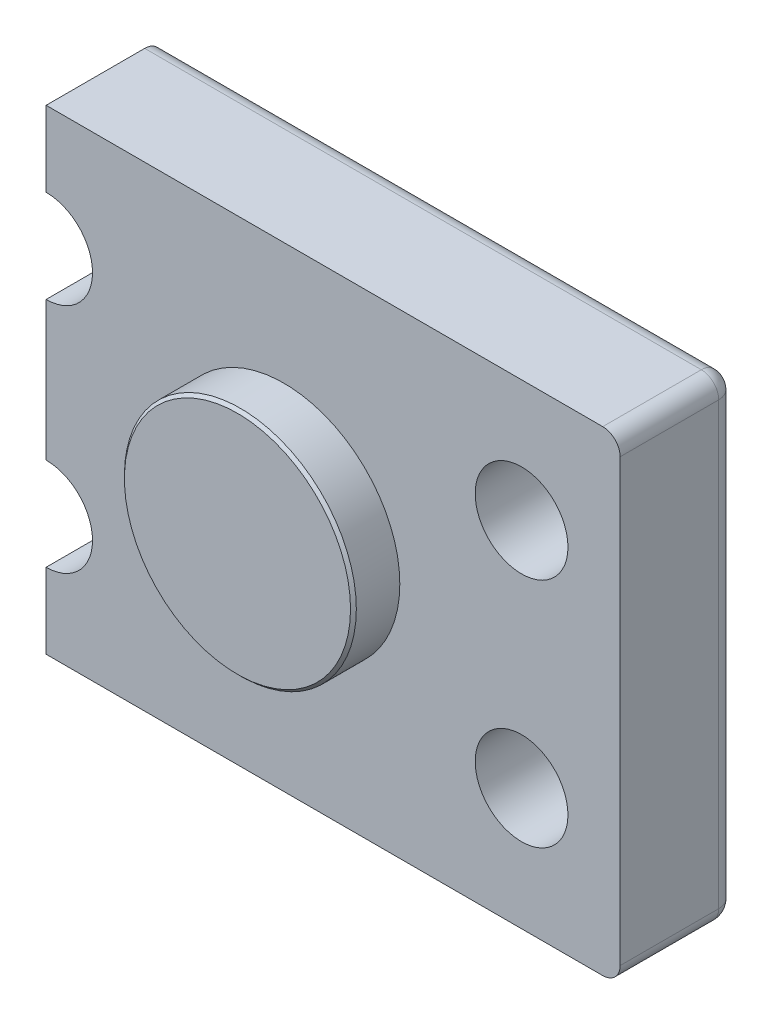
SolidWorks part; units mm, degrees
ref_plane "Front Plane" through (0, 0, 0) normal (0, 0, 1) x (1, 0, 0)
ref_plane "Top Plane" through (0, 0, 0) normal (0, 1, 0) x (1, 0, 0)
ref_plane "Right Plane" through (0, 0, 0) normal (1, 0, 0) x (0, 0, -1)
sketch "Sketch1" plane through (0, 0, 0) normal (0, 0, 1) x (1, 0, 0)
  line L0 (0, 69) -> (0, 82)
  line L1 (0, 0) -> (99, 0)
  line L2 (0, 0) -> (0, 13)
  line L3 (0, 82) -> (99, 82)
  line L4 (99, 0) -> (99, 82)
  line L5 (0, 29) -> (0, 53)
  arc A0 (0, 53) -> (0, 69) centre (0, 61) ccw
  arc A1 (0, 13) -> (0, 29) centre (0, 21) ccw
  point P8 (8, 21)
  dimension "D3" = 8
  dimension "D4" = 8
  dimension "D5" = 40
  dimension "D6" = 21
  dimension "D1" = 99
  dimension "D2" = 82
extrude "Boss-Extrude1" add sketch "Sketch1" along normal blind 20
sketch "Sketch2" plane through (0, 0, 20) normal (0, 0, 1) x (1, 0, 0)
  line L0 (0, 13) -> (0, 0) construction
  line L2 (0, 0) -> (99, 0) construction
  circle A0 centre (82, 21) radius 8
  arc A1 (0, 13) -> (0, 29) centre (0, 21) ccw construction
  point P9 (112.4625, 15.268)
  dimension "D1" = 82
  dimension "D2" = 21
extrude "Cut-Extrude1" cut sketch "Sketch2" against normal through all
pattern_linear "LPattern1" count 2 spacing 40 along (0, 1, 0) of "Cut-Extrude1"
sketch "Sketch3" plane through (0, 0, 20) normal (0, 0, 1) x (1, 0, 0)
  line L0 (0, 53) -> (0, 29) construction
  line L1 (0, 0) -> (99, 0) construction
  circle A0 centre (41, 41) radius 20
  dimension "D1" = 40
  dimension "D3" = 41
  dimension "D2" = 41
extrude "Boss-Extrude2" add sketch "Sketch3" along normal blind 8
chamfer "Chamfer1" distance 0.5 1 edges at (61, 41, 28)
fillet "Fillet1" radius 3 5 edges at (49.5, 0, 0) (49.5, 82, 0) (99, 41, 0) (99, 0, 10) (99, 82, 10)
